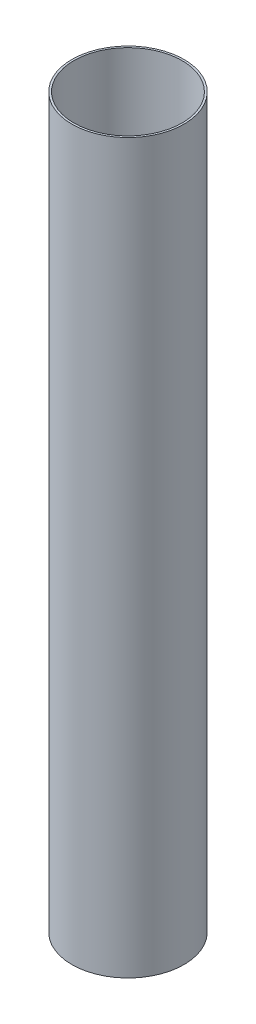
SolidWorks part; units mm, degrees
material "Corrugated Paper"
ref_plane "Front Plane" through (0, 0, 0) normal (0, 0, 1) x (1, 0, 0)
ref_plane "Top Plane" through (0, 0, 0) normal (0, 1, 0) x (1, 0, 0)
ref_plane "Right Plane" through (0, 0, 0) normal (1, 0, 0) x (0, 0, -1)
sketch "Sketch1" plane through (0, 0, 0) normal (0, 1, 0) x (1, 0, 0)
  circle A0 centre (0, 0) radius 27.5
  circle A1 centre (0, 0) radius 28.5
  dimension "D1" = 55
  dimension "D2" = 57
extrude "Boss-Extrude1" add sketch "Sketch1" along normal blind 370
